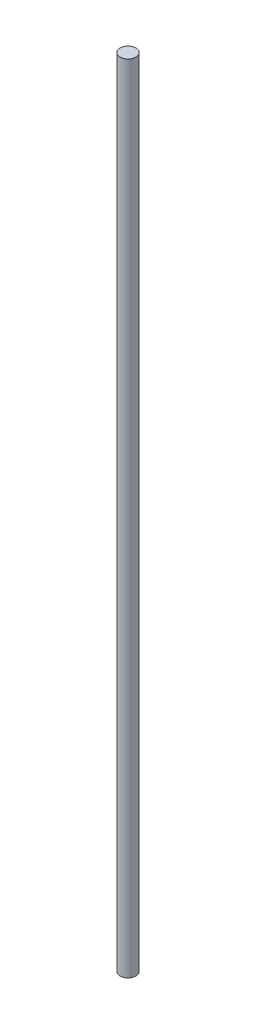
SolidWorks part; units mm, degrees
ref_plane "Front Plane" through (0, 0, 0) normal (0, 0, 1) x (1, 0, 0)
ref_plane "Top Plane" through (0, 0, 0) normal (0, 1, 0) x (1, 0, 0)
ref_plane "Right Plane" through (0, 0, 0) normal (1, 0, 0) x (0, 0, -1)
sketch "Sketch2" plane through (0, 0, 0) normal (0, 1, 0) x (1, 0, 0)
  circle A0 centre (0, 0) radius 4
  dimension "D1" = 8
extrude "Boss-Extrude1" add sketch "Sketch2" along normal mid plane 400
